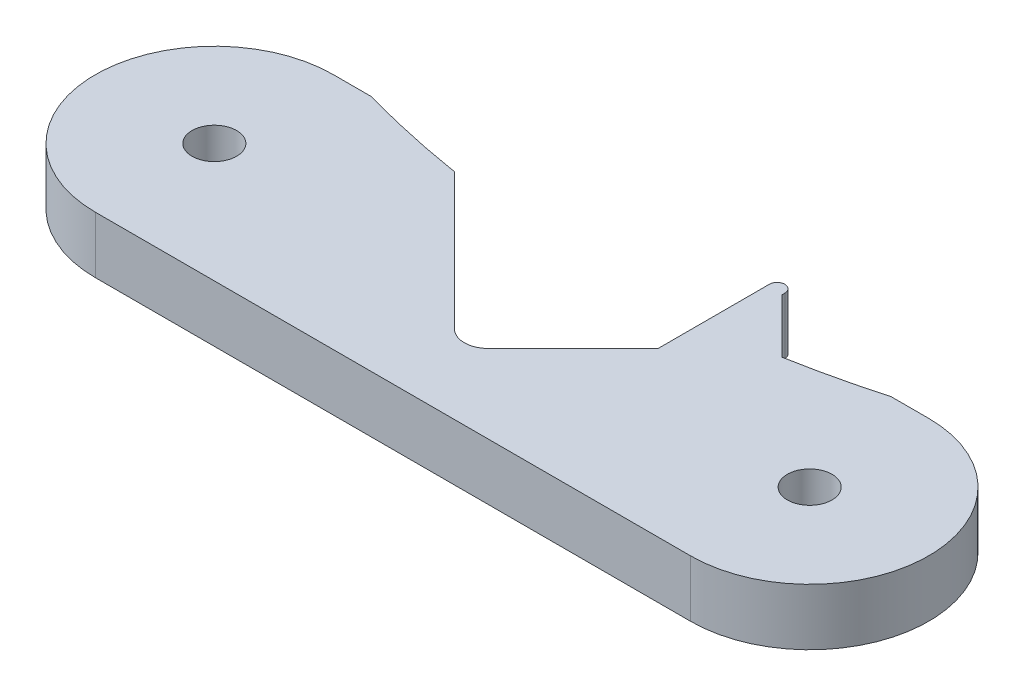
SolidWorks part; units mm, degrees
ref_plane "Front Plane" through (0, 0, 0) normal (0, 0, 1) x (1, 0, 0)
ref_plane "Top Plane" through (0, 0, 0) normal (0, 1, 0) x (1, 0, 0)
ref_plane "Right Plane" through (0, 0, 0) normal (1, 0, 0) x (0, 0, -1)
sketch "Sketch1" plane through (0, 0, 0) normal (0, 1, 0) x (1, 0, 0)
  line L0 (-25, -5) -> (25, -5) construction
  line L1 (-25, 5) -> (25, 5)
  line L2 (-25, -15) -> (25, -15)
  line L3 (0, -5) -> (0, 0) construction
  arc A0 (-25, 5) -> (-25, -15) centre (-25, -5) ccw
  arc A1 (25, -15) -> (25, 5) centre (25, -5) ccw
  circle A3 centre (-25, -5) radius 1.875
  circle A4 centre (25, -5) radius 1.875
  point P11 (0, 5)
  dimension "D3" = 5
  dimension "D5" = 3.75
  dimension "D2" = 50
  dimension "D1" = 20
  dimension "D6" = 50
  dimension "D7" = 5
extrude "Boss-Extrude1" add sketch "Sketch1" along normal blind 4.7625
sketch "Sketch3" plane through (0, 4.7625, 0) normal (0, 1, 0) x (1, 0, 0)
  line L0 (0, 0) -> (0, 2) construction
  line L1 (-12.855, 3.0266) -> (-1.4142, -8.4142)
  line L2 (1.4142, -8.4142) -> (12.855, 3.0266)
  arc A0 (12.855, 3.0266) -> (-12.855, 3.0266) centre (0, 83) ccw
  arc A1 (-1.4142, -8.4142) -> (1.4142, -8.4142) centre (0, -7) ccw
  dimension "D1" = 162
  dimension "D3" = 2
  dimension "D2" = 83
  dimension "D4" = 90
  dimension "D5" = 90
extrude "Cut-Extrude1" cut sketch "Sketch3" against normal through all
sketch "Sketch4" plane through (0, 4.7625, 0) normal (0, 1, 0) x (1, 0, 0)
  line L0 (14.3777, 3.2862) -> (8.5511, -1.2773)
  line L1 (1.4142, -8.4142) -> (12.855, 3.0266) construction
  line L2 (8.5511, 8.0628) -> (8.5511, -1.2773)
  line L3 (9.8511, 8.0628) -> (9.8511, 7.8128)
  line L4 (0, 83) -> (0, 0) construction
  line L5 (0, 83) -> (9.2011, 8.0628) construction
  line L6 (9.8511, 7.8128) -> (14.3777, 3.2862)
  arc A0 (8.5511, 8.0628) -> (9.8511, 8.0628) centre (9.2011, 8.0628) cw
  arc A2 (12.855, 3.0266) -> (21.8403, 5) centre (0, 83) ccw construction
  dimension "D5" = 0.65
  dimension "D2" = 0.25
  dimension "D3" = 75.5
  dimension "D4" = 7
  dimension "D6" = 45
extrude "Boss-Extrude2" add sketch "Sketch4" against normal up to surface (4.7625 mm away) up to face at (-25, 0, 6.875)
